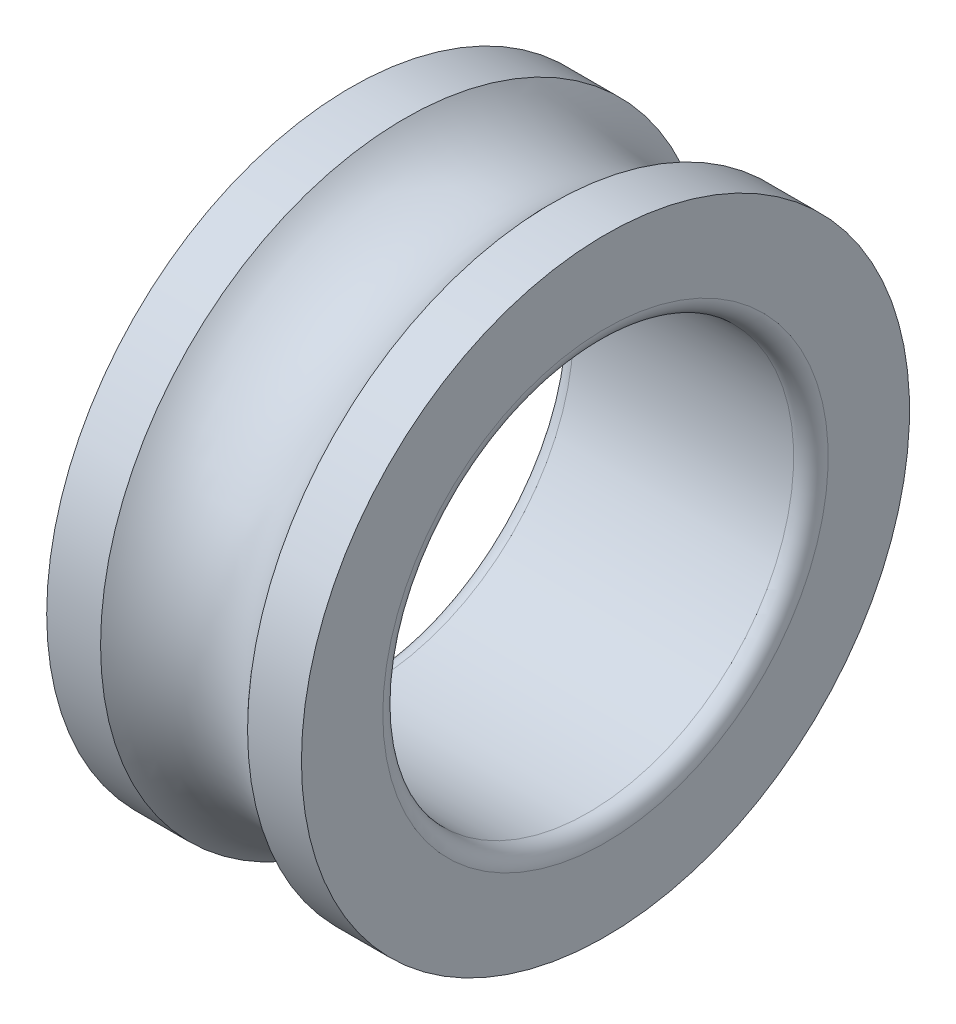
SolidWorks part; units mm, degrees
ref_plane "Front Plane" through (0, 0, 0) normal (0, 0, 1) x (1, 0, 0)
ref_plane "Top Plane" through (0, 0, 0) normal (0, 1, 0) x (1, 0, 0)
ref_plane "Right Plane" through (0, 0, 0) normal (1, 0, 0) x (0, 0, -1)
sketch "Sketch1" plane through (0, 0, 0) normal (0, 0, 1) x (1, 0, 0)
  line L0 (-27.1368, 0) -> (37.6068, 0) construction
  line L1 (0, 25) -> (0, 0) construction
  line L2 (-15.5, 37) -> (-8.9443, 37)
  line L3 (-15.5, 37) -> (-15.5, 27.1)
  line L4 (-13.4, 25) -> (13.4, 25)
  line L5 (15.5, 37) -> (15.5, 27.1)
  line L6 (-15.5, 37) -> (15.5, 25) construction
  line L7 (-15.5, 25) -> (15.5, 37) construction
  line L8 (8.9443, 37) -> (15.5, 37)
  arc A0 (8.9443, 37) -> (-8.9443, 37) centre (0, 45) cw
  arc A1 (13.4, 25) -> (15.5, 27.1) centre (13.4, 27.1) ccw
  arc A2 (-15.5, 27.1) -> (-13.4, 25) centre (-13.4, 27.1) ccw
  point P3 (0, 31)
  dimension "D5" = 12
  dimension "D6" = 2.1
  dimension "D1" = 25
  dimension "D2" = 37
  dimension "D3" = 31
  dimension "D4" = 8
revolve "Revolve1" add sketch "Sketch1" angle 360 about L0
